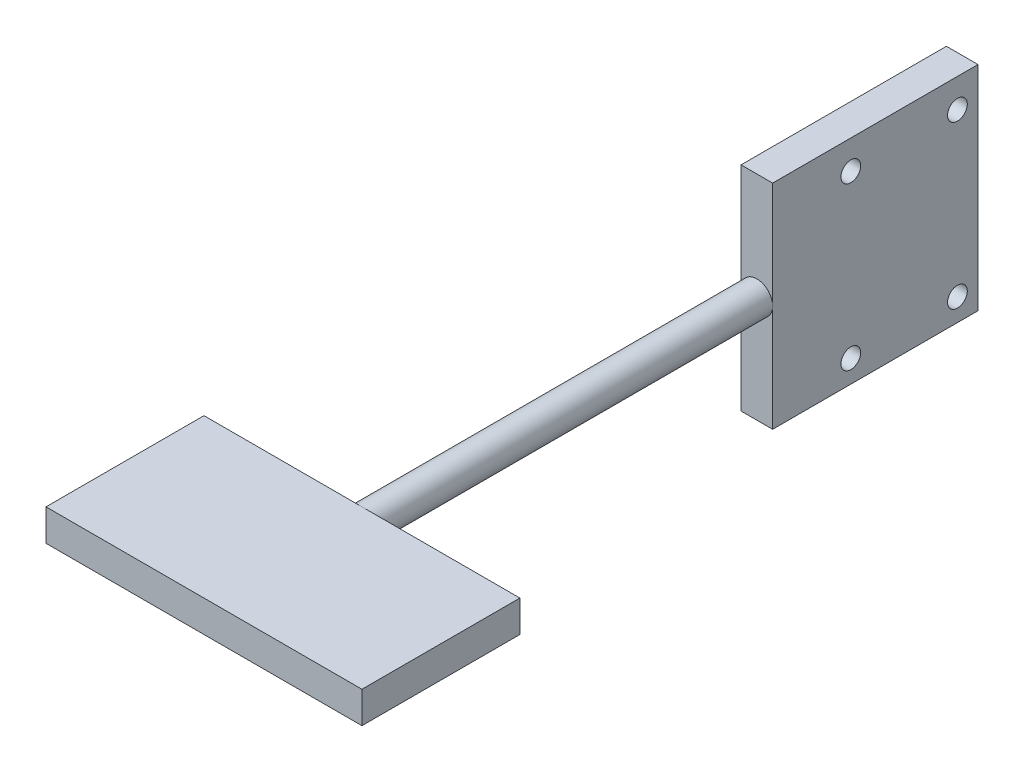
SolidWorks part; units mm, degrees
ref_plane "Front Plane" through (0, 0, 0) normal (0, 0, 1) x (1, 0, 0)
ref_plane "Top Plane" through (0, 0, 0) normal (0, 1, 0) x (1, 0, 0)
ref_plane "Right Plane" through (0, 0, 0) normal (1, 0, 0) x (0, 0, -1)
sketch "Sketch1" plane through (0, 0, 0) normal (0, 1, 0) x (1, 0, 0)
  line L1 (-12.8814, 10.1695) -> (27.1186, 10.1695)
  line L2 (-12.8814, 10.1695) -> (-12.8814, -9.8305)
  line L3 (-12.8814, -9.8305) -> (27.1186, -9.8305)
  line L4 (27.1186, 10.1695) -> (27.1186, -9.8305)
  dimension "D1" = 20
  dimension "D2" = 40
extrude "Boss-Extrude1" add sketch "Sketch1" along normal blind 4
sketch "Sketch3" plane through (0, 0, -10.1695) normal (0, 0, -1) x (-1, 0, 0)
  line L0 (12.8814, 4) -> (-27.1186, 0)
  line L1 (-27.1186, 0) -> (-27.1186, 4)
  line L2 (-27.1186, 4) -> (12.8814, 0)
  line L3 (12.8814, 4) -> (12.8814, 0) construction
  line L4 (-27.1186, 0) -> (12.8814, 0) construction
  circle A0 centre (-7.1186, 2) radius 2
  dimension "D1" = 4
extrude "Boss-Extrude3" add sketch "Sketch3" along normal blind 50 contours A0
sketch "Sketch4" plane through (0, 0, -60.1695) normal (0, 0, -1) x (-1, 0, 0)
  circle A1 centre (-7.1186, 2) radius 2
  circle A2 centre (-7.1186, 2) radius 2
  dimension "D1" = 0
ref_plane "Plane1" through (7.1186, 0, 0) normal (1, 0, 0) x (0, 0, -1)
sketch "Sketch5" plane through (7.1186, 0, 0) normal (1, 0, 0) x (0, 0, -1)
  line L0 (60.1695, 0) -> (60.1695, 4) construction
  line L1 (60.1695, 2) -> (86.1695, 2)
  line L2 (60.1695, 2) -> (60.1695, 15.5)
  line L3 (60.1695, 15.5) -> (86.1695, 15.5)
  line L4 (86.1695, 2) -> (86.1695, 15.5)
  line L6 (60.1695, 2) -> (86.1695, 2)
  line L7 (60.1695, 2) -> (60.1695, -11.5)
  line L8 (60.1695, -11.5) -> (86.1695, -11.5)
  line L9 (86.1695, 2) -> (86.1695, -11.5)
  dimension "D1" = 26
  dimension "D2" = 26
  dimension "D3" = 13.5
  dimension "D4" = 13.5
extrude "Boss-Extrude4" add sketch "Sketch5" along normal blind 2 contours L1 L4 L3 L2 | L9 L1 L7 L8
sketch "Sketch6" plane through (7.1186, 0, 0) normal (-1, 0, 0) x (0, 0, 1)
  line L6 (-60.1695, -11.5) -> (-60.1695, 0)
  line L7 (-60.1695, 0) -> (-60.1695, 4)
  line L8 (-60.1695, 4) -> (-60.1695, 15.5)
  line L9 (-60.1695, 15.5) -> (-86.1695, 15.5)
  line L10 (-86.1695, 15.5) -> (-86.1695, -11.5)
  line L11 (-86.1695, -11.5) -> (-60.1695, -11.5)
  line L12 (-60.1695, -11.5) -> (-60.1695, 0)
  line L13 (-60.1695, 0) -> (-60.1695, 4)
  line L14 (-60.1695, 4) -> (-60.1695, 15.5)
  line L15 (-60.1695, 15.5) -> (-86.1695, 15.5)
  line L16 (-86.1695, 15.5) -> (-86.1695, -11.5)
  line L17 (-86.1695, -11.5) -> (-60.1695, -11.5)
  dimension "D1" = 0
extrude "Boss-Extrude5" add sketch "Sketch6" along normal blind 2
sketch "Sketch7" plane through (5.1186, 0, 0) normal (-1, 0, 0) x (0, 0, 1)
  line L2 (-60.1695, 1.5) -> (-86.1695, 15)
  line L8 (-86.1695, -11.5) -> (-60.1695, -11.5)
  line L9 (-60.1695, -11.5) -> (-60.1695, 2)
  line L10 (-60.1695, 15.5) -> (-86.1695, 15.5)
  line L11 (-86.1695, 15.5) -> (-86.1695, -11.5)
  line L14 (-60.1695, 15.5) -> (-86.1695, 15.5)
  line L15 (-86.1695, 15.5) -> (-86.1695, -11.5)
  line L17 (-60.1695, 2) -> (-60.1695, 15.5)
  line L18 (-60.1695, 2) -> (-60.1695, 15.5)
  circle A0 centre (-83.565, -8.655) radius 1.25
  circle A1 centre (-70.065, 11.845) radius 1.25
  circle A2 centre (-70.065, -8.655) radius 1.25
  circle A3 centre (-83.565, 11.845) radius 1.25
  dimension "D1" = 0
extrude "Cut-Extrude1" cut sketch "Sketch7" against normal through all contours A3 | A1 | A2 | A0
